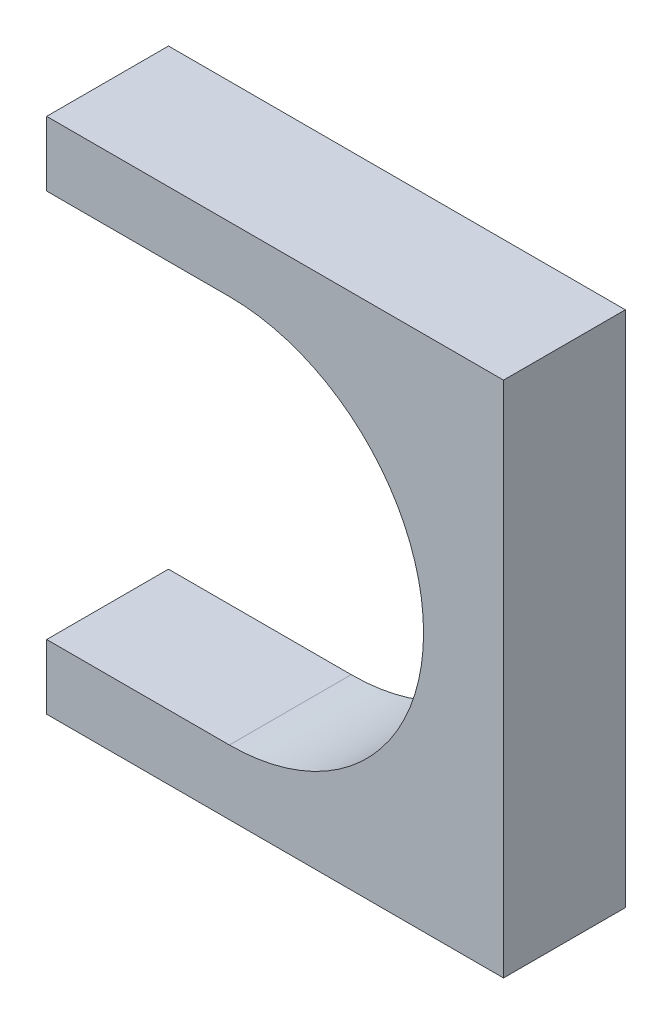
SolidWorks part; units mm, degrees
ref_plane "Front Plane" through (0, 0, 0) normal (0, 0, 1) x (1, 0, 0)
ref_plane "Top Plane" through (0, 0, 0) normal (0, 1, 0) x (1, 0, 0)
ref_plane "Right Plane" through (0, 0, 0) normal (1, 0, 0) x (0, 0, -1)
sketch "스케치1" plane through (0, 0, 0) normal (0, 0, 1) x (1, 0, 0)
  circle A0 centre (0, 0) radius 17
  dimension "D1" = 34
extrude "보스-돌출1" add sketch "스케치1" along normal blind 8
sketch "스케치3" plane through (0, 0, 8) normal (0, 0, 1) x (1, 0, 0)
  line L0 (0, 0) -> (-50000, 0) construction
  line L1 (0, 0) -> (0, 50000) construction
  line L3 (18, 17) -> (-12, 17)
  line L4 (18, 17) -> (18, -17)
  line L5 (18, -17) -> (-12, -17)
  line L6 (-12, 17) -> (-12, -17)
  dimension "D1" = 18
  dimension "D2" = 30
  dimension "D3" = 17
  dimension "D4" = 34
extrude "보스-돌출2" add sketch "스케치3" against normal blind 8
sketch "스케치2" plane through (0, 0, 8) normal (0, 0, 1) x (1, 0, 0)
  circle A0 centre (0, 0) radius 12.75
  dimension "D1" = 25.5
extrude "컷-돌출1" cut sketch "스케치2" against normal blind 8
sketch "스케치4" plane through (0, 0, 0) normal (0, 0, -1) x (-1, 0, 0)
  line L0 (0, 0) -> (0, 50000) construction
  line L1 (0, 0) -> (50000, 0) construction
  line L3 (0, 12.75) -> (50000, 12.75) construction
  line L4 (0, -12.75) -> (50000, -12.75) construction
  line L6 (0, 12.75) -> (19.9046, 12.75)
  line L7 (0, 12.75) -> (0, -12.75)
  line L8 (0, -12.75) -> (19.9046, -12.75)
  line L9 (19.9046, 12.75) -> (19.9046, -12.75)
extrude "컷-돌출2" cut sketch "스케치4" against normal blind 8
